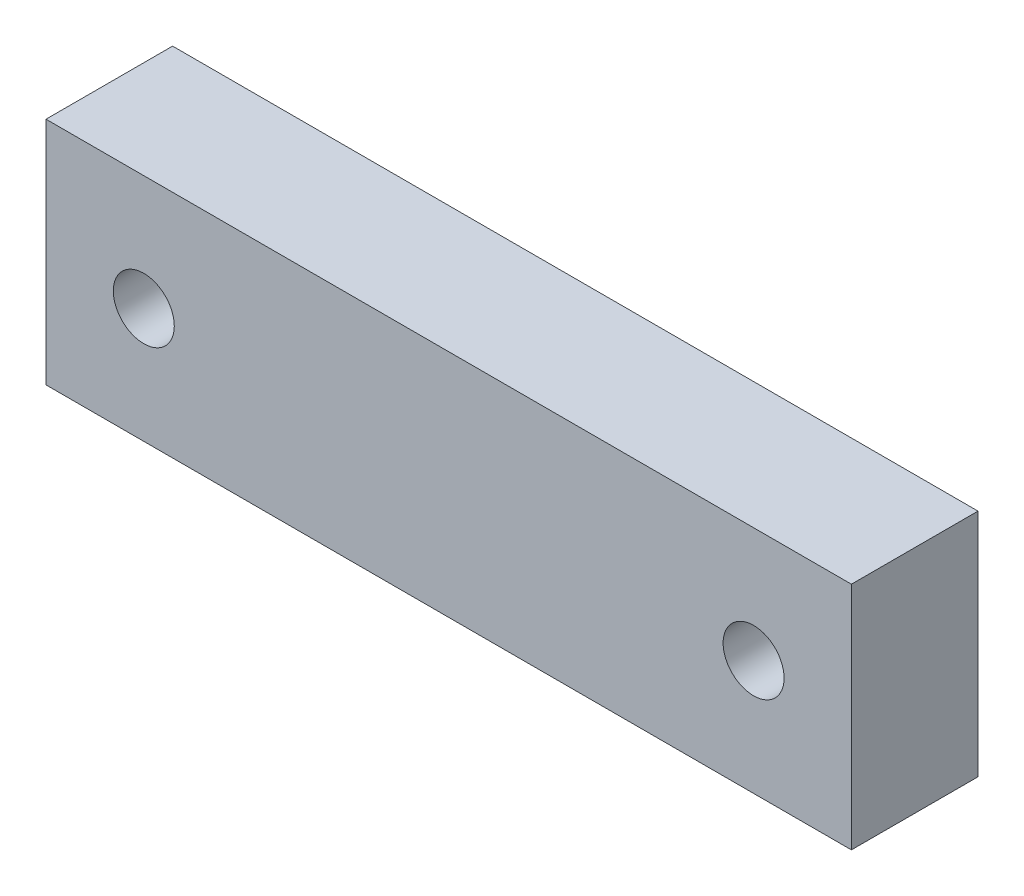
SolidWorks part; units mm, degrees
material "ABS"
ref_plane "Front Plane" through (0, 0, 0) normal (0, 0, 1) x (1, 0, 0)
ref_plane "Top Plane" through (0, 0, 0) normal (0, 1, 0) x (1, 0, 0)
ref_plane "Right Plane" through (0, 0, 0) normal (1, 0, 0) x (0, 0, -1)
sketch "Sketch1" plane through (0, 0, 0) normal (0, 0, 1) x (1, 0, 0)
  line L0 (75, -42.5) -> (-75, -42.5) construction
  line L1 (-35, -42.5) -> (35, -42.5)
  line L2 (-35, -42.5) -> (-35, -62.5)
  line L3 (-35, -62.5) -> (35, -62.5)
  line L4 (35, -42.5) -> (35, -62.5)
  line L5 (95, -62.5) -> (-95, -62.5) construction
  line L8 (-45, -62.5) -> (-45, -42.5) construction
  line L9 (45, -42.5) -> (45, -62.5) construction
  circle A0 centre (26.5, -52.5) radius 2.65 construction
  circle A1 centre (-26.5, -52.5) radius 2.65 construction
  circle A2 centre (26.5, -52.5) radius 2.65
  circle A3 centre (-26.5, -52.5) radius 2.65
  dimension "D1" = 10
  dimension "D2" = 10
extrude "Extrude1" add sketch "Sketch1" along normal up to vertex (11.0029 mm away)
